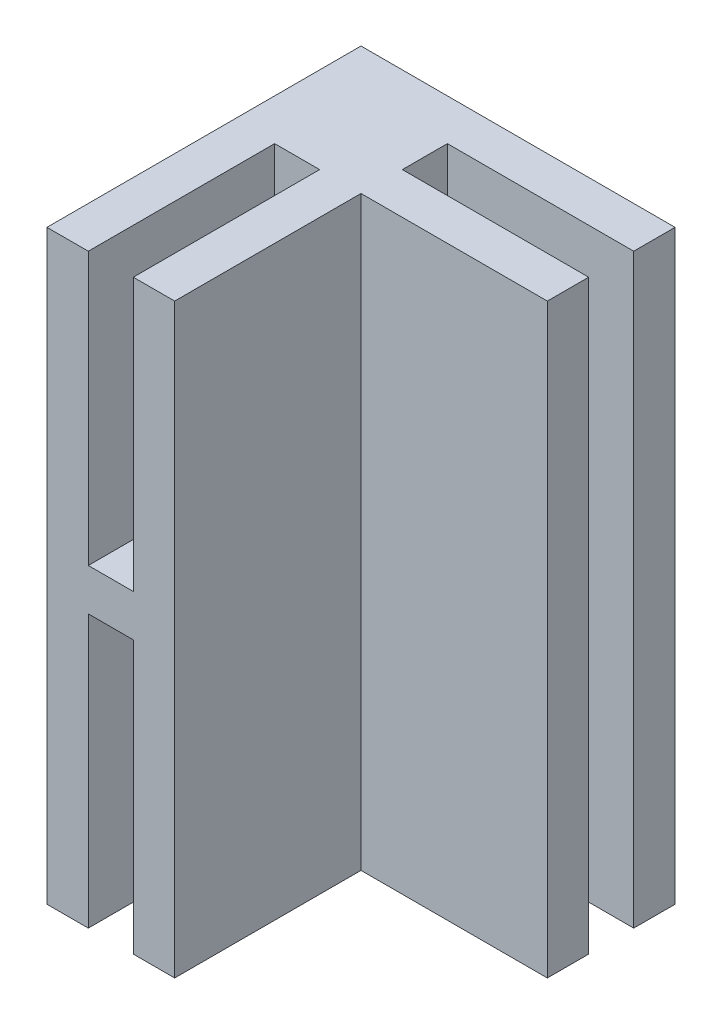
SolidWorks part; units mm, degrees
ref_plane "Plan de face" through (0, 0, 0) normal (0, 0, 1) x (1, 0, 0)
ref_plane "Plan de dessus" through (0, 0, 0) normal (0, 1, 0) x (1, 0, 0)
ref_plane "Plan de droite" through (0, 0, 0) normal (1, 0, 0) x (0, 0, -1)
sketch "Esquisse1" plane through (0, 0, 0) normal (0, 1, 0) x (1, 0, 0)
  line L1 (-11.3793, 9.3842) -> (18.6207, 9.3842)
  line L2 (-11.3793, 9.3842) -> (-11.3793, -20.6158)
  line L3 (-11.3793, -20.6158) -> (18.6207, -20.6158)
  line L4 (18.6207, 9.3842) -> (18.6207, -20.6158)
  dimension "D1" = 30
  dimension "D2" = 30
extrude "Boss.-Extru.1" add sketch "Esquisse1" along normal blind 56
sketch "Esquisse2" plane through (0, 0, 0) normal (0, -1, 0) x (1, 0, 0)
  line L0 (18.6207, 20.6158) -> (18.6207, -9.3842) construction
  line L5 (18.6207, -5.4342) -> (0.8207, -5.4342)
  line L6 (18.6207, -5.4342) -> (18.6207, -1.1342)
  line L7 (18.6207, -1.1342) -> (0.8207, -1.1342)
  line L8 (0.8207, -5.4342) -> (0.8207, -1.1342)
  line L15 (18.6207, -9.3842) -> (-11.3793, -9.3842) construction
  line L21 (18.6207, 20.6158) -> (0.8207, 20.6158)
  line L22 (18.6207, 20.6158) -> (18.6207, 2.8158)
  line L23 (18.6207, 2.8158) -> (0.8207, 2.8158)
  line L24 (0.8207, 20.6158) -> (0.8207, 2.8158)
  dimension "D1" = 4.3
  dimension "D2" = 3.95
  dimension "D3" = 17.8
  dimension "D4" = 3.95
extrude "Enlèv. mat.-Extru.1" cut sketch "Esquisse2" against normal through all
sketch "Esquisse3" plane through (0, 0, 0) normal (0, -1, 0) x (1, 0, 0)
  line L8 (-11.3793, 20.6158) -> (0.8207, 20.6158) construction
  line L9 (-3.1293, 20.6158) -> (-7.4293, 20.6158)
  line L10 (-3.1293, 20.6158) -> (-3.1293, 2.8158)
  line L11 (-3.1293, 2.8158) -> (-7.4293, 2.8158)
  line L12 (-7.4293, 20.6158) -> (-7.4293, 2.8158)
  line L14 (-11.3793, -9.3842) -> (-11.3793, 20.6158) construction
  dimension "D1" = 4.3
  dimension "D2" = 17.8
  dimension "D4" = 3.95
extrude "Enlèv. mat.-Extru.2" cut sketch "Esquisse3" against normal blind 26
sketch "Esquisse6" plane through (0, 56, 0) normal (0, 1, 0) x (1, 0, 0)
  line L0 (-11.3793, -20.6158) -> (0.8207, -20.6158) construction
  line L1 (-7.4293, -20.6158) -> (-3.1293, -20.6158)
  line L2 (-7.4293, -20.6158) -> (-7.4293, -2.8158)
  line L3 (-7.4293, -2.8158) -> (-3.1293, -2.8158)
  line L4 (-3.1293, -20.6158) -> (-3.1293, -2.8158)
  line L5 (-11.3793, 9.3842) -> (-11.3793, -20.6158) construction
  dimension "D1" = 4.3
  dimension "D2" = 3.95
  dimension "D3" = 17.8
extrude "Enlèv. mat.-Extru.4" cut sketch "Esquisse6" against normal blind 26
